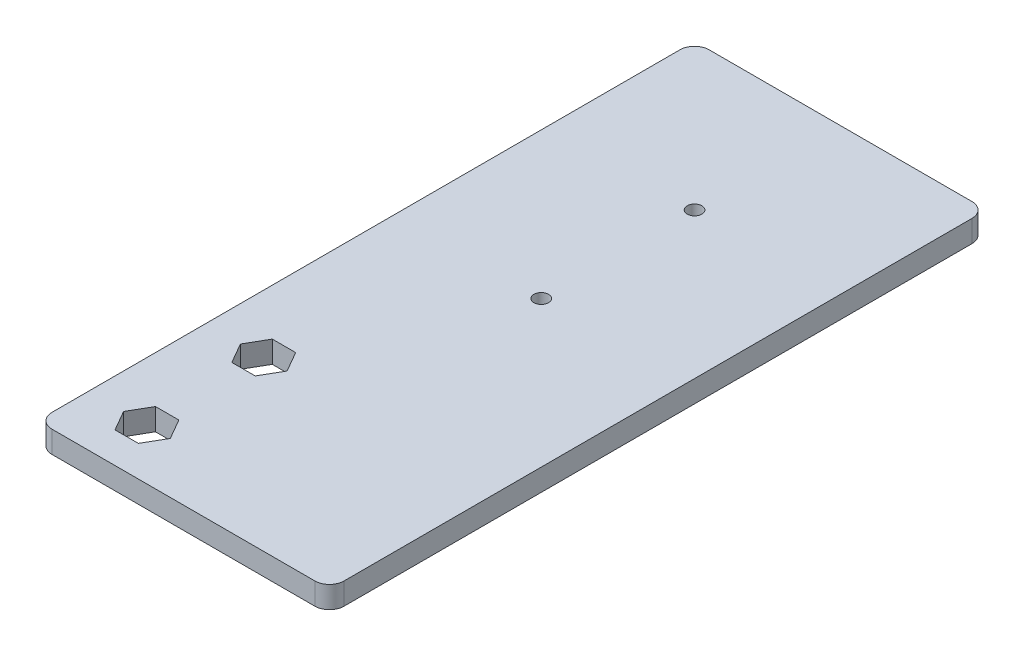
SolidWorks part; units mm, degrees
ref_plane "Plan de face" through (0, 0, 0) normal (0, 0, 1) x (1, 0, 0)
ref_plane "Plan de dessus" through (0, 0, 0) normal (0, 1, 0) x (1, 0, 0)
ref_plane "Plan de droite" through (0, 0, 0) normal (1, 0, 0) x (0, 0, -1)
sketch "Esquisse1" plane through (0, 0, 0) normal (0, 1, 0) x (1, 0, 0)
  line L5 (13, 2) -> (13, 88)
  line L7 (15, 0) -> (51, 0)
  line L8 (53, 88) -> (53, 2)
  line L11 (15, 90) -> (51, 90)
  arc A0 (51, 90) -> (53, 88) centre (51, 88) cw
  arc A1 (15, 0) -> (13, 2) centre (15, 2) cw
  arc A2 (51, 0) -> (53, 2) centre (51, 2) ccw
  arc A3 (15, 90) -> (13, 88) centre (15, 88) ccw
  point P12 (53, 90)
  point P15 (13, 0)
  point P26 (13, 90)
  dimension "D3" = 2
  dimension "D5" = 2
  dimension "D1" = 90
  dimension "D2" = 40
  dimension "D4" = 13
extrude "Extrusion1" add sketch "Esquisse1" along normal blind 3
sketch "Esquisse2" plane through (0, 0, 0) normal (0, -1, 0) x (1, 0, 0)
  line L0 (13, -88) -> (13, -2) construction
  line L1 (15, 0) -> (51, 0) construction
  circle A14 centre (21, -7) radius 1.1
  circle A15 centre (21, -23) radius 1.1
  dimension "D4" = 2.2
  dimension "D5" = 2.2
  dimension "D1" = 8
  dimension "D2" = 16
  dimension "D3" = 7
extrude "Enlèv. mat.-Extru.1" cut sketch "Esquisse2" against normal through all
sketch "Esquisse3" plane through (0, 3, 0) normal (0, 1, 0) x (1, 0, 0)
  line L0 (15, 0) -> (51, 0) construction
  line L1 (17.8, 23) -> (19.4, 20.2287)
  line L2 (19.4, 20.2287) -> (22.6, 20.2287)
  line L3 (22.6, 20.2287) -> (24.2, 23)
  line L4 (24.2, 23) -> (22.6, 25.7713)
  line L5 (22.6, 25.7713) -> (19.4, 25.7713)
  line L6 (19.4, 25.7713) -> (17.8, 23)
  line L7 (17.8, 7) -> (19.4, 4.2287)
  line L8 (19.4, 4.2287) -> (22.6, 4.2287)
  line L9 (22.6, 4.2287) -> (24.2, 7)
  line L10 (24.2, 7) -> (22.6, 9.7713)
  line L11 (22.6, 9.7713) -> (19.4, 9.7713)
  line L12 (19.4, 9.7713) -> (17.8, 7)
  line L13 (13, 88) -> (13, 2) construction
  line L15 (51, 90) -> (15, 90) construction
  circle A0 centre (21, 23) radius 2.7713 construction
  circle A1 centre (21, 7) radius 2.7713 construction
  circle A2 centre (33, 70) radius 1
  circle A3 centre (33, 49) radius 1
  point P28 (33.1525, 90)
  point P29 (0, 0)
  dimension "D6" = 2
  dimension "D1" = 3.2
  dimension "D2" = 3.2
  dimension "D3" = 20
  dimension "D4" = 20
  dimension "D5" = 21
extrude "Enlèv. mat.-Extru.2" cut sketch "Esquisse3" against normal through all
